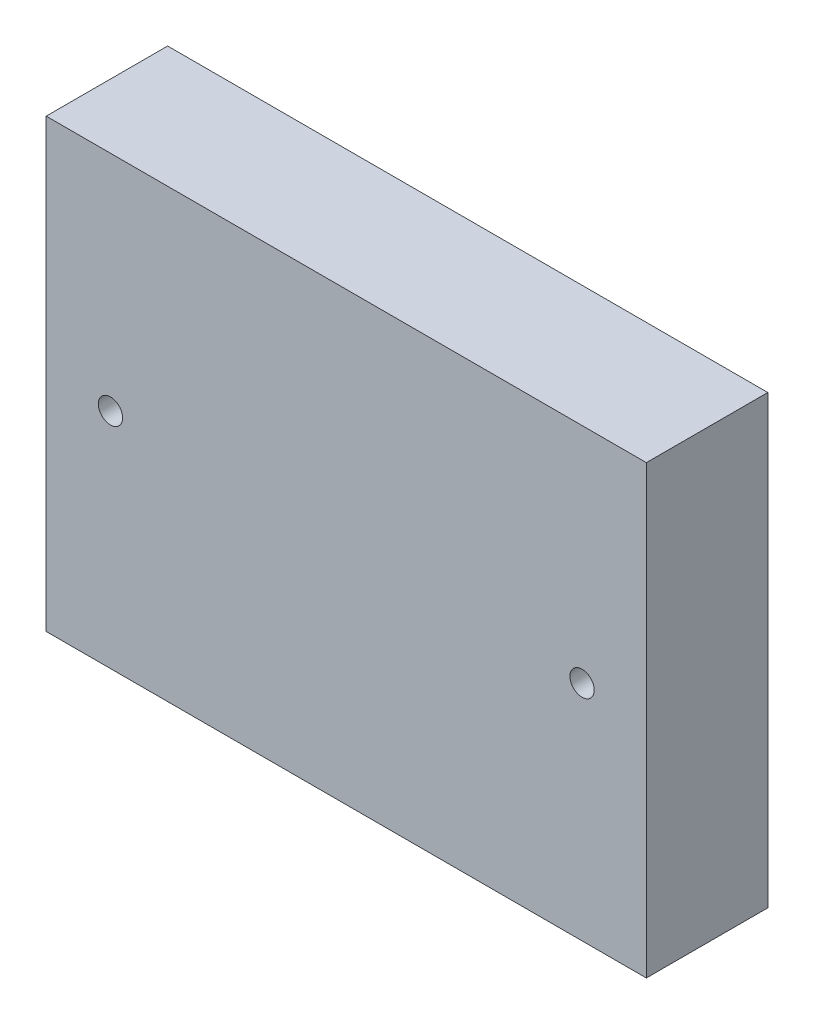
SolidWorks part; units mm, degrees
ref_plane "Front Plane" through (0, 0, 0) normal (0, 0, 1) x (1, 0, 0)
ref_plane "Top Plane" through (0, 0, 0) normal (0, 1, 0) x (1, 0, 0)
ref_plane "Right Plane" through (0, 0, 0) normal (1, 0, 0) x (0, 0, -1)
sketch "Sketch1" plane through (0, 0, 0) normal (0, 0, 1) x (1, 0, 0)
  line L1 (0, 0) -> (47.0662, 0)
  line L2 (0, 0) -> (0, 35.0012)
  line L3 (0, 35.0012) -> (47.0662, 35.0012)
  line L4 (47.0662, 0) -> (47.0662, 35.0012)
  dimension "D1" = 35.0012
  dimension "D2" = 47.0662
extrude "Boss-Extrude1" add sketch "Sketch1" along normal blind 9.525
sketch "Sketch2" plane through (0, 0, 0) normal (0, 0, -1) x (-1, 0, 0)
  line L0 (-47.0662, 17.5006) -> (-43.8531, 17.5006) construction
  line L3 (-47.0662, 0) -> (-47.0662, 35.0012) construction
  line L4 (-43.8531, 17.5006) -> (-3.2131, 17.5006) construction
  line L5 (-3.2131, 17.5006) -> (0, 17.5006) construction
  line L6 (0, 35.0012) -> (0, 0) construction
  line L7 (-23.5331, 35.0012) -> (-23.5331, 0) construction
  line L8 (-47.0662, 35.0012) -> (0, 35.0012) construction
  line L9 (0, 0) -> (-47.0662, 0) construction
  circle A0 centre (-5.0419, 17.5006) radius 0.9525
  circle A1 centre (-42.0243, 17.5006) radius 0.9525
  dimension "D3" = 1.905
  dimension "D1" = 40.64
  dimension "D2" = 1.8288
extrude "Cut-Extrude1" cut sketch "Sketch2" against normal through all
